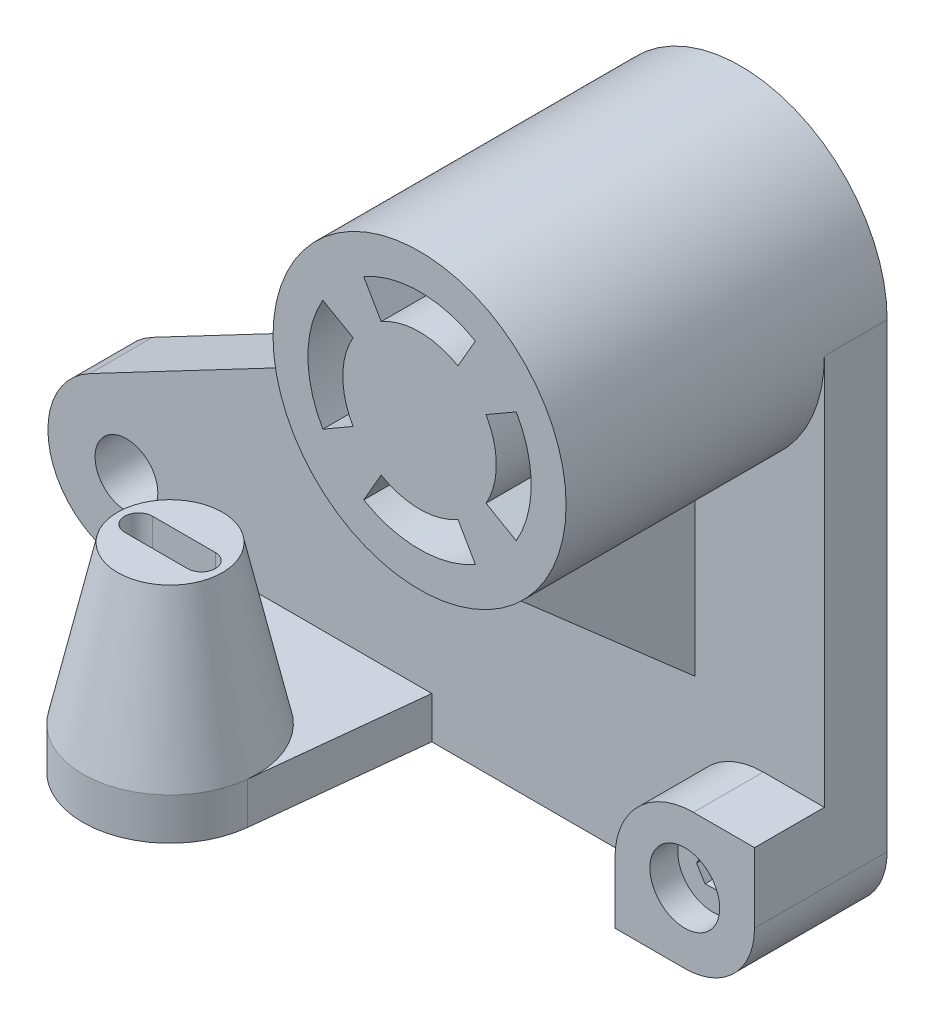
SolidWorks part; units mm, degrees
ref_plane "Ön Düzlem" through (0, 0, 0) normal (0, 0, 1) x (1, 0, 0)
ref_plane "Üst Düzlem" through (0, 0, 0) normal (0, 1, 0) x (1, 0, 0)
ref_plane "Sağ Düzlem" through (0, 0, 0) normal (1, 0, 0) x (0, 0, -1)
sketch "Çizim1" plane through (0, 0, 0) normal (0, 0, 1) x (1, 0, 0)
  line L0 (-32.4115, 0) -> (147.5885, 0)
  line L1 (167.5885, 20) -> (167.5885, 152)
  line L9 (83.5885, 152) -> (83.5885, 106.7185)
  line L10 (38.2853, 84) -> (60.87, 84)
  line L11 (-42.8913, 42.4104) -> (32.2731, 81.9728)
  arc A0 (147.5885, 0) -> (167.5885, 20) centre (147.5885, 20) ccw
  arc A3 (-42.8913, 42.4104) -> (-32.4115, 0) centre (-32.4115, 22.5) ccw
  arc A4 (60.87, 84) -> (83.5885, 106.7185) centre (60.87, 106.7185) ccw
  circle A6 centre (48.5885, 64) radius 9
  arc A7 (32.2731, 81.9728) -> (38.2853, 84) centre (41.5885, 64.2747) cw
  circle A8 centre (-32.4115, 22.5) radius 9
  arc A9 (83.5885, 152) -> (167.5885, 152) centre (125.5885, 152) ccw
  dimension "D3" = 20
  dimension "D4" = 22.5
  dimension "D6" = 20
  dimension "D7" = 42
  dimension "D8" = 18
  dimension "D11" = 18
  dimension "D1" = 200
  dimension "D2" = 152
  dimension "D9" = 84
  dimension "D10" = 35
extrude "Yükseklik-Ekstrüzyon1" add sketch "Çizim1" along normal blind 18
sketch "Çizim2" plane through (0, 0, 0) normal (0, 0, 1) x (1, 0, 0)
  circle A0 centre (125.5885, 152) radius 42
extrude "Yükseklik-Ekstrüzyon2" add sketch "Çizim2" along normal blind 92
sketch "Çizim3" plane through (0, 0, 18) normal (0, 0, 1) x (1, 0, 0)
  line L0 (127.5885, 0) -> (127.5885, 17.5101)
  line L1 (-32.4115, 0) -> (147.5885, 0) construction
  line L2 (150.0783, 40) -> (167.5885, 40)
  line L3 (167.5885, 20) -> (167.5885, 152) construction
  line L4 (127.5885, 0) -> (147.5885, 0)
  line L5 (167.5885, 20) -> (167.5885, 40)
  arc A1 (127.5885, 17.5101) -> (150.0783, 40) centre (150.0783, 17.5101) cw
  arc A2 (147.5885, 0) -> (167.5885, 20) centre (147.5885, 20) ccw construction
  arc A3 (147.5885, 0) -> (167.5885, 20) centre (147.5885, 20) ccw
  point P9 (167.4679, 40)
  dimension "D1" = 40
  dimension "D2" = 40
extrude "Yükseklik-Ekstrüzyon3" add sketch "Çizim3" along normal blind 20
sketch "Çizim4" plane through (0, 0, 38) normal (0, 0, 1) x (1, 0, 0)
  line L0 (167.5885, 40) -> (150.0783, 40) construction
  line L1 (145.4074, 15.9286) -> (150.0238, 16.0754)
  line L2 (150.0238, 16.0754) -> (152.2049, 20.1468)
  line L3 (152.2049, 20.1468) -> (149.7695, 24.0714)
  line L4 (149.7695, 24.0714) -> (145.1531, 23.9246)
  line L5 (145.1531, 23.9246) -> (142.972, 19.8532)
  line L6 (142.972, 19.8532) -> (145.4074, 15.9286)
  line L8 (127.5885, 17.5101) -> (127.5885, 0) construction
  circle A1 centre (147.5885, 20) radius 4 construction
  dimension "D1" = 8
  dimension "D2" = 20
  dimension "D3" = 20
extrude "Kes-Ekstrüzyon1" cut sketch "Çizim4" against normal blind 60
sketch "Çizim5" plane through (0, 0, 92) normal (0, 0, 1) x (1, 0, 0)
  line L0 (125.5885, 112.6348) -> (125.5885, 130) construction
  line L1 (136.5885, 171.0526) -> (141.5885, 179.7128)
  line L2 (114.5885, 171.0526) -> (109.5885, 179.7128)
  line L3 (125.5885, 174) -> (125.5885, 188.7683) construction
  line L4 (144.641, 141) -> (153.3013, 136)
  line L5 (144.641, 163) -> (153.3013, 168)
  line L6 (114.5885, 132.9474) -> (109.5885, 124.2872)
  line L7 (136.5885, 132.9474) -> (141.5885, 124.2872)
  line L8 (106.5359, 163) -> (97.8756, 168)
  line L9 (106.5359, 141) -> (97.8756, 136)
  arc A0 (141.5885, 179.7128) -> (109.5885, 179.7128) centre (125.5885, 152) ccw
  arc A1 (136.5885, 171.0526) -> (114.5885, 171.0526) centre (125.5885, 152) ccw
  arc A2 (144.641, 141) -> (144.641, 163) centre (125.5885, 152) ccw
  arc A3 (153.3013, 136) -> (153.3013, 168) centre (125.5885, 152) ccw
  arc A4 (114.5885, 132.9474) -> (136.5885, 132.9474) centre (125.5885, 152) ccw
  arc A5 (109.5885, 124.2872) -> (141.5885, 124.2872) centre (125.5885, 152) ccw
  arc A6 (106.5359, 163) -> (106.5359, 141) centre (125.5885, 152) ccw
  arc A7 (97.8756, 168) -> (97.8756, 136) centre (125.5885, 152) ccw
  point P25 (125.5885, 152)
  dimension "D1" = 44
  dimension "D2" = 64
  dimension "D3" = 60
  dimension "D4" = 30
  dimension "D5" = 4
extrude "Kes-Ekstrüzyon2" cut sketch "Çizim5" against normal blind 108
ref_plane "Düzlem1" through (125.59, 0, 0) normal (1, 0, 0) x (0, 0, -1)
sketch "Çizim6" plane through (125.59, 0, 0) normal (1, 0, 0) x (0, 0, -1)
  line L0 (-82, 110) -> (-18, 54)
  line L1 (-18, 40) -> (-18, 152) construction
  line L2 (-38, 0) -> (0, 0) construction
  line L3 (-92, 110) -> (-18, 110) construction
  point P7 (0, 0)
  point P8 (-75.2435, 110)
  dimension "D1" = 54
  dimension "D2" = 64
rib "Feder1" sketch "Çizim6" sketch "Çizim6" thickness 10 extrusion direction parallel to sketch draft on no parameters "D1"=10
sketch "Çizim7" plane through (0, 0, 0) normal (0, 1, 0) x (1, 0, 0)
  line L0 (-4.9115, -18) -> (0.2327, -65.6816)
  line L1 (-32.4115, -18) -> (127.5885, -18) construction
  line L2 (-54.9115, 0) -> (-54.9115, -18) construction
  line L3 (49.9442, -65.6816) -> (55.0885, -18)
  line L4 (-4.9115, -18) -> (55.0885, -18)
  arc A0 (0.2327, -65.6816) -> (49.9442, -65.6816) centre (25.0885, -63) ccw
  dimension "D2" = 50
  dimension "D1" = 50
  dimension "D4" = 60
  dimension "D5" = 30
  dimension "D6" = 45
extrude "Yükseklik-Ekstrüzyon4" add sketch "Çizim7" along normal blind 12
ref_plane "Düzlem2" through (0, 57, 0) normal (0, 1, 0) x (1, 0, 0)
sketch "Çizim8" plane through (0, 57, 0) normal (0, 1, 0) x (1, 0, 0)
  circle A0 centre (25.0885, -63) radius 15
  dimension "D1" = 30
sketch "Çizim9" plane through (0, 12, 0) normal (0, 1, 0) x (1, 0, 0)
  circle A0 centre (25.0885, -63) radius 25
  dimension "D1" = 50
loft "Loft1" add profiles "Çizim9", "Çizim8"
sketch "Çizim10" plane through (0, 57, 0) normal (0, 1, 0) x (1, 0, 0)
  line L0 (16.0885, -63) -> (34.0885, -63) construction
  line L1 (16.0885, -59) -> (34.0885, -59)
  line L2 (16.0885, -67) -> (34.0885, -67)
  arc A0 (16.0885, -59) -> (16.0885, -67) centre (16.0885, -63) ccw
  arc A1 (34.0885, -67) -> (34.0885, -59) centre (34.0885, -63) ccw
  circle A3 centre (25.0885, -63) radius 15 construction
  point P3 (25.0885, -63)
  point P8 (0, 0)
  point P10 (25.9056, -63)
  dimension "D2" = 4
  dimension "D1" = 18
extrude "Kes-Ekstrüzyon3" cut sketch "Çizim10" against normal blind 65
sketch "Çizim11" plane through (0, 0, 38) normal (0, 0, 1) x (1, 0, 0)
  line L0 (167.5885, 40) -> (150.0783, 40) construction
  line L1 (127.5885, 17.5101) -> (127.5885, 0) construction
  circle A0 centre (147.5885, 20) radius 10
  dimension "D1" = 20
  dimension "D3" = 20
  dimension "D2" = 20
extrude "Kes-Ekstrüzyon4" cut sketch "Çizim11" against normal blind 8
